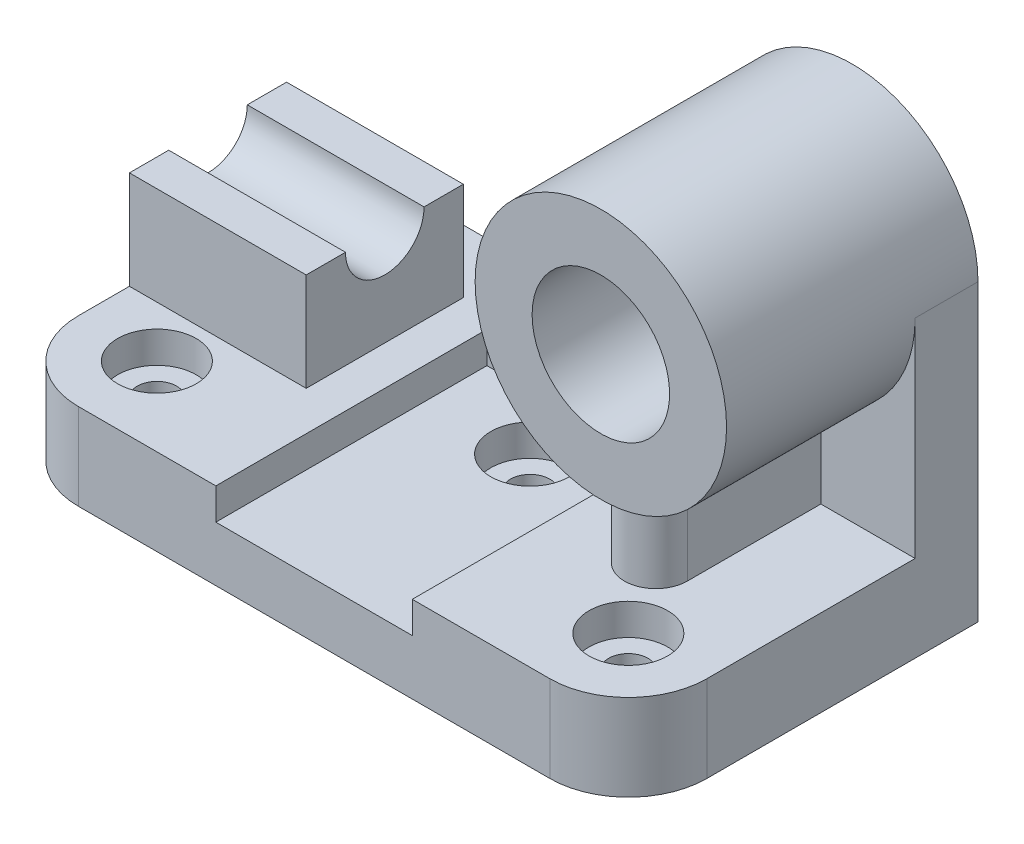
SolidWorks part; units mm, degrees
ref_plane "Alzado" through (0, 0, 0) normal (0, 0, 1) x (1, 0, 0)
ref_plane "Planta" through (0, 0, 0) normal (0, 1, 0) x (1, 0, 0)
ref_plane "Vista lateral" through (0, 0, 0) normal (1, 0, 0) x (0, 0, -1)
sketch "Croquis2" plane through (0, 0, 0) normal (0, 1, 0) x (1, 0, 0)
  line L0 (20, 0) -> (140, 0)
  line L1 (160, 20) -> (160, 89)
  line L2 (160, 89) -> (0, 89)
  line L3 (0, 89) -> (0, 20)
  arc A0 (140, 0) -> (160, 20) centre (140, 20) ccw
  arc A1 (0, 20) -> (20, 0) centre (20, 20) ccw
  circle A2 centre (20, 20) radius 5
  circle A3 centre (140, 20) radius 5
  circle A4 centre (80, 55) radius 5
  dimension "D3" = 20
  dimension "D4" = 20
  dimension "D5" = 10
  dimension "D7" = 10
  dimension "D8" = 10
  dimension "D1" = 160
  dimension "D2" = 89
  dimension "D6" = 80
  dimension "D9" = 55
extrude "Saliente-Extruir1" add sketch "Croquis2" along normal blind 22
sketch "Croquis3" plane through (0, 22, 0) normal (0, 1, 0) x (1, 0, 0)
  line L0 (55, 0) -> (55, 69)
  line L1 (20, 0) -> (140, 0) construction
  line L2 (55, 69) -> (105, 69)
  line L3 (105, 69) -> (105, 0)
  line L4 (105, 0) -> (55, 0)
  line L5 (0, 89) -> (0, 20) construction
  circle A0 centre (20, 20) radius 10
  circle A1 centre (140, 20) radius 10
  dimension "D4" = 20
  dimension "D5" = 20
  dimension "D1" = 50
  dimension "D2" = 55
  dimension "D3" = 69
extrude "Cortar-Extruir1" cut sketch "Croquis3" against normal blind 8
sketch "Croquis4" plane through (0, 14, 0) normal (0, 1, 0) x (1, 0, 0)
  circle A0 centre (80, 55) radius 10
  dimension "D1" = 20
extrude "Cortar-Extruir2" cut sketch "Croquis4" against normal blind 8
ref_plane "Plano1" through (0, 75, 0) normal (0, 1, 0) x (1, 0, 0)
sketch "Croquis5" plane through (0, 75, 0) normal (0, 1, 0) x (1, 0, 0)
  line L0 (160, 89) -> (145.5, 89)
  line L1 (160, 89) -> (0, 89) construction
  line L2 (145.5, 89) -> (145.5, 25)
  line L3 (145.5, 25) -> (160, 25)
  line L4 (160, 20) -> (160, 89) construction
  line L5 (160, 25) -> (160, 89)
  line L6 (128, 107.3974) -> (128, 35.4075) construction
  dimension "D1" = 64
  dimension "D2" = 32
  dimension "D3" = 17.5
revolve "Revolución1" add sketch "Croquis5" angle 360 about L6
sketch "Croquis8" plane through (0, 22, 0) normal (0, 1, 0) x (1, 0, 0)
  line L0 (96, 89) -> (96, 73)
  line L1 (96, 89) -> (96, 25) construction
  line L2 (96, 73) -> (120, 73)
  line L3 (120, 73) -> (120, 39)
  line L4 (136, 39) -> (136, 73)
  line L5 (136, 73) -> (160, 73)
  line L6 (160, 25) -> (160, 89) construction
  line L7 (160, 73) -> (160, 89)
  line L8 (160, 89) -> (96, 89)
  arc A0 (120, 39) -> (136, 39) centre (128, 39) ccw
  dimension "D3" = 8
  dimension "D1" = 16
  dimension "D2" = 16
  dimension "D4" = 50
  dimension "D5" = 32
extrude "Saliente-Extruir2" add sketch "Croquis8" along normal up to next
sketch "Croquis9" plane through (0, 22, 0) normal (0, 1, 0) x (1, 0, 0)
  line L0 (0, 73) -> (45, 73)
  line L1 (0, 89) -> (0, 20) construction
  line L2 (45, 73) -> (45, 33)
  line L3 (45, 33) -> (0, 33)
  line L4 (0, 33) -> (0, 73)
  dimension "D1" = 40
  dimension "D2" = 16
  dimension "D3" = 45
extrude "Saliente-Extruir3" add sketch "Croquis9" along normal blind 25
sketch "Croquis10" plane through (0, 47, 0) normal (0, 1, 0) x (1, 0, 0)
  line L0 (0, 53) -> (0, 63)
  line L1 (0, 73) -> (0, 33) construction
  line L2 (0, 63) -> (45, 63)
  line L3 (45, 33) -> (45, 73) construction
  line L4 (45, 63) -> (45, 53)
  line L5 (45, 33) -> (45, 73) construction
  line L6 (45, 53) -> (0, 53)
  dimension "D1" = 10
revolve "Cortar-Revolución1" cut sketch "Croquis10" angle 360 about L6
sketch "Croquis11" plane through (0, 22, 0) normal (0, 1, 0) x (1, 0, 0)
  line L0 (10, 89) -> (10, 73)
  line L1 (96, 89) -> (0, 89) construction
  line L2 (45, 73) -> (0, 73) construction
  line L3 (10, 73) -> (0, 73)
  line L4 (0, 73) -> (0, 89)
  line L5 (0, 89) -> (10, 89)
  dimension "D1" = 10
